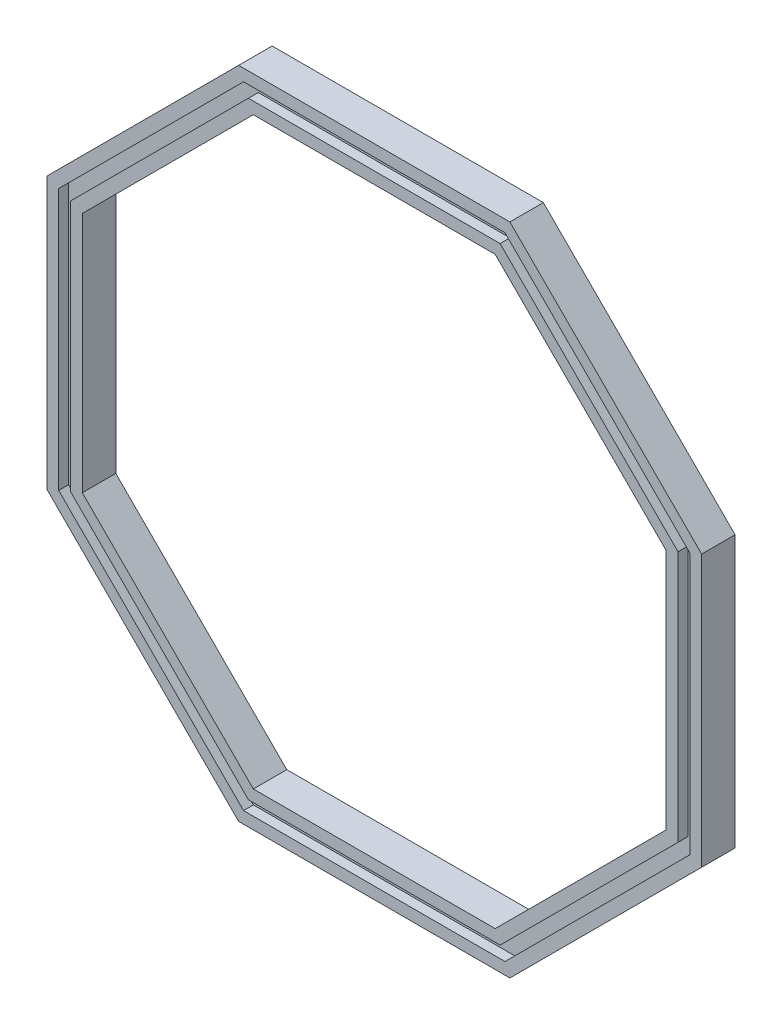
SolidWorks part; units mm, degrees
other "마크업1"
sketch "스케치11"
other "마크업2"
sketch "스케치12" plane through (34.9216, -34.9216, 0) normal (0.0999, -0.4002, 0.911) x (0.9947, 0.0186, -0.1009)
ref_plane "정면" through (0, 0, 0) normal (0, 0, 1) x (1, 0, 0)
ref_plane "윗면" through (0, 0, 0) normal (0, 1, 0) x (1, 0, 0)
ref_plane "우측면" through (0, 0, 0) normal (1, 0, 0) x (0, 0, -1)
sketch "스케치7" plane through (0, 0, 0) normal (0, 0, 1) x (1, 0, 0)
  line L0 (55, 0) -> (-55, 0) construction
  line L1 (13.2795, -32.0597) -> (32.0597, -13.2795)
  line L2 (32.0597, -13.2795) -> (32.0597, 13.2795)
  line L3 (32.0597, 13.2795) -> (13.2795, 32.0597)
  line L4 (13.2795, 32.0597) -> (-13.2795, 32.0597)
  line L5 (-13.2795, 32.0597) -> (-32.0597, 13.2795)
  line L6 (-32.0597, 13.2795) -> (-32.0597, -13.2795)
  line L7 (-32.0597, -13.2795) -> (-13.2795, -32.0597)
  line L8 (-13.2795, -32.0597) -> (13.2795, -32.0597)
  line L9 (13.7766, -33.2597) -> (33.2597, -13.7766)
  line L10 (33.2597, -13.7766) -> (33.2597, 13.7766)
  line L11 (33.2597, 13.7766) -> (13.7766, 33.2597)
  line L12 (13.7766, 33.2597) -> (-13.7766, 33.2597)
  line L13 (-13.7766, 33.2597) -> (-33.2597, 13.7766)
  line L14 (-33.2597, 13.7766) -> (-33.2597, -13.7766)
  line L15 (-33.2597, -13.7766) -> (-13.7766, -33.2597)
  line L16 (-13.7766, -33.2597) -> (13.7766, -33.2597)
  line L17 (12.7825, -30.8597) -> (30.8597, -12.7825)
  line L18 (30.8597, -12.7825) -> (30.8597, 12.7825)
  line L19 (30.8597, 12.7825) -> (12.7825, 30.8597)
  line L20 (12.7825, 30.8597) -> (-12.7825, 30.8597)
  line L21 (-12.7825, 30.8597) -> (-30.8597, 12.7825)
  line L22 (-30.8597, 12.7825) -> (-30.8597, -12.7825)
  line L23 (-30.8597, -12.7825) -> (-12.7825, -30.8597)
  line L24 (-12.7825, -30.8597) -> (12.7825, -30.8597)
  line L25 (12.2854, -29.6597) -> (29.6597, -12.2854)
  line L26 (29.6597, -12.2854) -> (29.6597, 12.2854)
  line L27 (29.6597, 12.2854) -> (12.2854, 29.6597)
  line L28 (12.2854, 29.6597) -> (-12.2854, 29.6597)
  line L29 (-12.2854, 29.6597) -> (-29.6597, 12.2854)
  line L30 (-29.6597, 12.2854) -> (-29.6597, -12.2854)
  line L31 (-29.6597, -12.2854) -> (-12.2854, -29.6597)
  line L32 (-12.2854, -29.6597) -> (12.2854, -29.6597)
  circle A0 centre (0, 0) radius 34.7011 construction
  dimension "D1" = 72
  dimension "D4" = 1.2
  dimension "D2" = 1.2
  dimension "D3" = 1.2
extrude "보스-돌출2" add sketch "스케치7" against normal blind 3.4 contours L23 L24 L17 L18 L19 L20 L21 L22 L32 L31 L30 L29 L28 L27 L26 L25 | L7 L8 L1 L2 L3 L4 L5 L6 L24 L23 L22 L21 L20 L19 L18 L17 | L15 L16 L9 L10 L11 L12 L13 L14 L8 L7 L6 L5 L4 L3 L2 L1
sketch "스케치9" plane through (0, 0, 0) normal (0, 0, 1) x (1, 0, 0)
  line L0 (29.6597, -12.2854) -> (29.6597, 12.2854) construction
  line L1 (13.2795, -32.0597) -> (32.0597, -13.2795)
  line L2 (32.0597, -13.2795) -> (32.0597, 13.2795)
  line L3 (32.0597, 13.2795) -> (13.2795, 32.0597)
  line L4 (13.2795, 32.0597) -> (-13.2795, 32.0597)
  line L5 (-13.2795, 32.0597) -> (-32.0597, 13.2795)
  line L6 (-32.0597, 13.2795) -> (-32.0597, -13.2795)
  line L7 (-32.0597, -13.2795) -> (-13.2795, -32.0597)
  line L8 (-13.2795, -32.0597) -> (13.2795, -32.0597)
  line L9 (13.7766, -33.2597) -> (33.2597, -13.7766) construction
  line L10 (12.7825, -30.8597) -> (30.8597, -12.7825)
  line L11 (30.8597, -12.7825) -> (30.8597, 12.7825)
  line L12 (30.8597, 12.7825) -> (12.7825, 30.8597)
  line L13 (12.7825, 30.8597) -> (-12.7825, 30.8597)
  line L14 (-12.7825, 30.8597) -> (-30.8597, 12.7825)
  line L15 (-30.8597, 12.7825) -> (-30.8597, -12.7825)
  line L16 (-30.8597, -12.7825) -> (-12.7825, -30.8597)
  line L17 (-12.7825, -30.8597) -> (12.7825, -30.8597)
  circle A0 centre (0, 0) radius 34.7011 construction
  circle A1 centre (0, 0) radius 33.4023 construction
  dimension "D1" = 1.2
  dimension "D2" = 1.2
extrude "컷-돌출3" cut sketch "스케치9" against normal blind 1
ref_plane "평면2" through (0, 0, -1.7) normal (0, 0, 1) x (1, 0, 0)
mirror "대칭 복사4" about plane through (0, 0, -1.7) normal (0, 0, 1) of "컷-돌출3"
